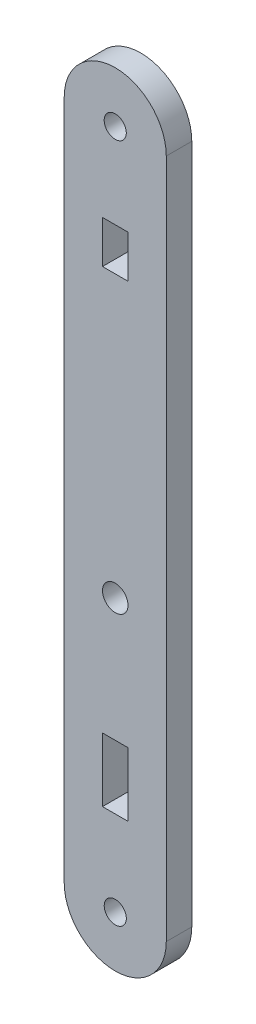
SolidWorks part; units mm, degrees
ref_plane "Front Plane" through (0, 0, 0) normal (0, 0, 1) x (1, 0, 0)
ref_plane "Top Plane" through (0, 0, 0) normal (0, 1, 0) x (1, 0, 0)
ref_plane "Right Plane" through (0, 0, 0) normal (1, 0, 0) x (0, 0, -1)
sketch "Model" plane through (0, 0, 0) normal (0, 0, 1) x (1, 0, 0)
  line L0 (49.144, 78.2316) -> (49.144, -1.7684)
  line L1 (53.644, 68.2316) -> (56.644, 68.2316)
  line L2 (56.644, 63.2316) -> (53.644, 63.2316)
  line L3 (56.644, 15.7316) -> (53.644, 15.7316)
  line L4 (56.644, 8.2316) -> (53.644, 8.2316)
  line L5 (53.644, 8.2316) -> (53.644, 15.7316)
  line L6 (56.644, 8.2316) -> (56.644, 15.7316)
  line L7 (56.644, 63.2316) -> (56.644, 68.2316)
  line L8 (53.644, 68.2316) -> (53.644, 63.2316)
  line L9 (61.144, -1.7685) -> (61.144, 78.2316)
  circle A0 centre (55.144, 30.2315) radius 1.5
  circle A1 centre (55.1472, -1.7614) radius 1.3
  circle A2 centre (55.144, 78.2316) radius 1.3
  arc A3 (61.144, 78.2316) -> (49.144, 78.2316) centre (55.144, 78.2316) ccw
  arc A4 (49.144, -1.7684) -> (61.144, -1.7685) centre (55.144, -1.7685) ccw
  point P20 (49.1455, -1.9039)
extrude "Boss-Extrude1" add sketch "Model" along normal blind 3
